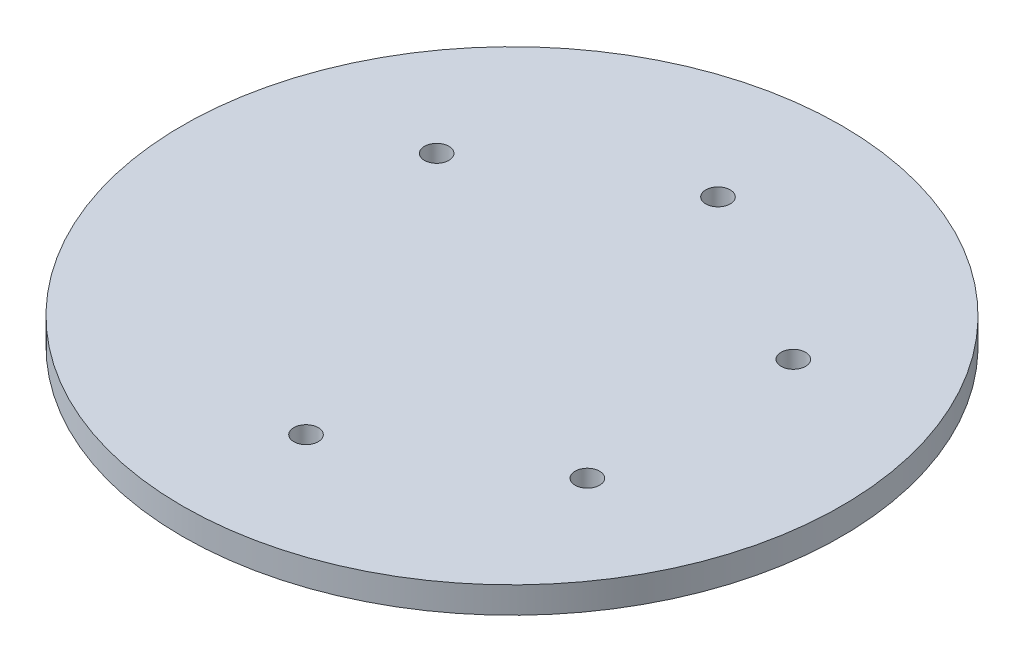
SolidWorks part; units mm, degrees
ref_plane "Front Plane" through (0, 0, 0) normal (0, 0, 1) x (1, 0, 0)
ref_plane "Top Plane" through (0, 0, 0) normal (0, 1, 0) x (1, 0, 0)
ref_plane "Right Plane" through (0, 0, 0) normal (1, 0, 0) x (0, 0, -1)
sketch "Sketch1" plane through (0, 0, 0) normal (0, 1, 0) x (1, 0, 0)
  circle A0 centre (0, 0) radius 20
extrude "Boss-Extrude1" add sketch "Sketch1" against normal blind 1.6
sketch "Sketch2" plane through (0, -1.6, 0) normal (0, -1, 0) x (1, 0, 0)
  line L1 (0.1408, 12.2934) -> (-0.1442, 12.7042) construction
  circle A6 centre (-0.0017, 12.4988) radius 0.743
  circle A7 centre (10.8234, 6.2509) radius 0.743
  circle A8 centre (10.8251, -6.2479) radius 0.743
  circle A9 centre (0.0017, -12.4988) radius 0.743
  circle A10 centre (-10.8234, -6.2509) radius 0.743
  circle A12 centre (-10.8251, 6.2479) radius 0.743 [skipped]
  point P17 (0, 0)
  point P18 (0, 0)
  dimension "D1" = 6
extrude "Cut-Extrude2" cut sketch "Sketch2" against normal blind 1.6
